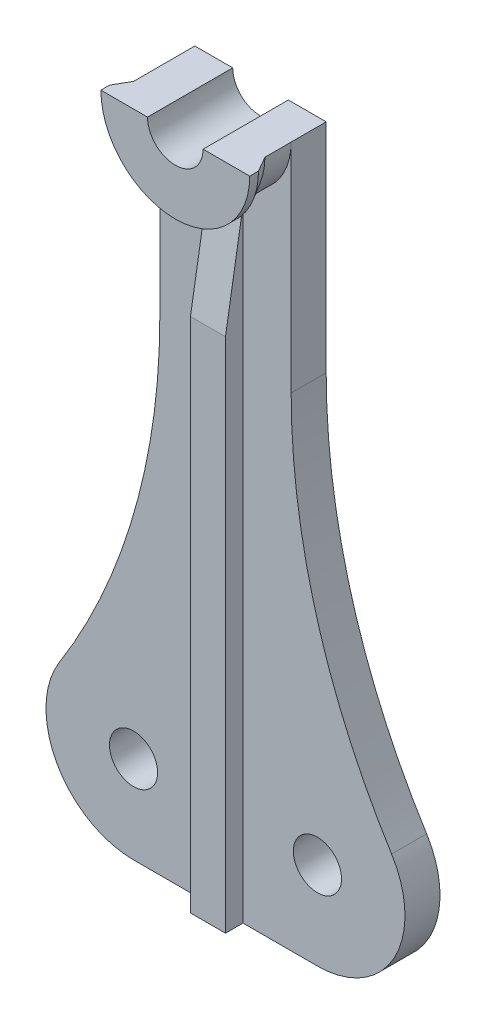
SolidWorks part; units mm, degrees
ref_plane "Front Plane" through (0, 0, 0) normal (0, 0, 1) x (1, 0, 0)
ref_plane "Top Plane" through (0, 0, 0) normal (0, 1, 0) x (1, 0, 0)
ref_plane "Right Plane" through (0, 0, 0) normal (1, 0, 0) x (0, 0, -1)
sketch "Sketch1" plane through (0, 0, 0) normal (0, 0, 1) x (1, 0, 0)
  line L0 (-10.5, -70) -> (10.5, -70) construction
  line L1 (0, 0) -> (0, -70) construction
  line L2 (-10.5, -60) -> (-7.5, -60)
  line L3 (10.5, -80) -> (-10.5, -80)
  line L4 (-7.5, 0) -> (-7.5, -60)
  line L5 (7.5, 0) -> (7.5, -60)
  line L6 (7.5, -60) -> (10.5, -60)
  line L7 (-7.5, 0) -> (-3.175, 0)
  line L8 (3.175, 0) -> (7.5, 0)
  arc A0 (-3.175, 0) -> (3.175, 0) centre (0, 0) ccw
  arc A1 (-10.5, -60) -> (-10.5, -80) centre (-10.5, -70) ccw
  arc A2 (10.5, -80) -> (10.5, -60) centre (10.5, -70) ccw
  circle A3 centre (-10.5, -70) radius 2.75
  circle A4 centre (10.5, -70) radius 2.75
  dimension "D1" = 20
  dimension "D2" = 5.5
  dimension "D5" = 6.35
  dimension "D6" = 15
  dimension "D3" = 21
  dimension "D4" = 70
extrude "Boss-Extrude1" add sketch "Sketch1" along normal blind 4
sketch "Sketch2" plane through (0, 0, 0) normal (0, 1, 0) x (1, 0, 0)
  line L0 (0, 0) -> (0, -12.208) construction
  line L1 (7.5, -4) -> (3.175, -4) construction
  line L2 (7.5, -4) -> (3.175, -4)
  line L3 (3.175, -4) -> (3.175, -9.7321)
  line L4 (3.175, -9.7321) -> (8.5, -9.7321)
  line L5 (8.5, -9.7321) -> (8.5, -8.7321)
  line L6 (8.5, -8.7321) -> (7.5, -7)
  line L7 (7.5, -7) -> (7.5, -4)
  dimension "D1" = 3
  dimension "D2" = 30
  dimension "D3" = 1
  dimension "D4" = 17
revolve "Revolve1" add sketch "Sketch2" angle 180 about L0
sketch "Sketch3" plane through (0, 0, 0) normal (1, 0, 0) x (0, 0, -1)
  line L0 (-4, -9) -> (-6, -21)
  line L1 (-4, -60) -> (-4, 0) construction
  line L2 (-6, -21) -> (-6, -80)
  line L3 (-6, -80) -> (-4, -80)
  line L4 (-4, -80) -> (-4, -9)
  line L5 (-4, 0) -> (0, 0) construction
  dimension "D1" = 2
  dimension "D2" = 9
  dimension "D3" = 12
extrude "Boss-Extrude2" add sketch "Sketch3" along normal mid plane 4
sketch "Sketch4" plane through (0, 0, 4) normal (0, 0, 1) x (1, 0, 0)
  line L0 (7.5, -60) -> (7.5, 0) construction
  line L1 (-7.5, 0) -> (-7.5, -60) construction
  line L2 (-7.5, -60) -> (-10.5, -60) construction
  line L3 (10.5, -60) -> (7.5, -60) construction
  line L4 (-7.5, -60) -> (-10.5, -60)
  line L5 (-7.5, -24.8226) -> (-7.5, -60)
  line L6 (7.5, -60) -> (7.5, -24.8226)
  line L7 (10.5, -60) -> (7.5, -60)
  arc A0 (-18.9706, -64.685) -> (-7.5, -24.8226) centre (-82.5, -24.8226) ccw
  arc A1 (7.5, -24.8226) -> (18.9706, -64.685) centre (82.5, -24.8226) ccw
  arc A2 (10.5, -80) -> (10.5, -60) centre (10.5, -70) ccw construction
  arc A3 (-10.5, -60) -> (-10.5, -80) centre (-10.5, -70) ccw construction
  arc A4 (-10.5, -60) -> (-18.9706, -64.685) centre (-10.5, -70) ccw
  arc A5 (18.9706, -64.685) -> (10.5, -60) centre (10.5, -70) ccw
  dimension "D1" = 150
extrude "Boss-Extrude3" add sketch "Sketch4" against normal up to surface (4 mm away) up to face at (-7.75, -70, 0)
